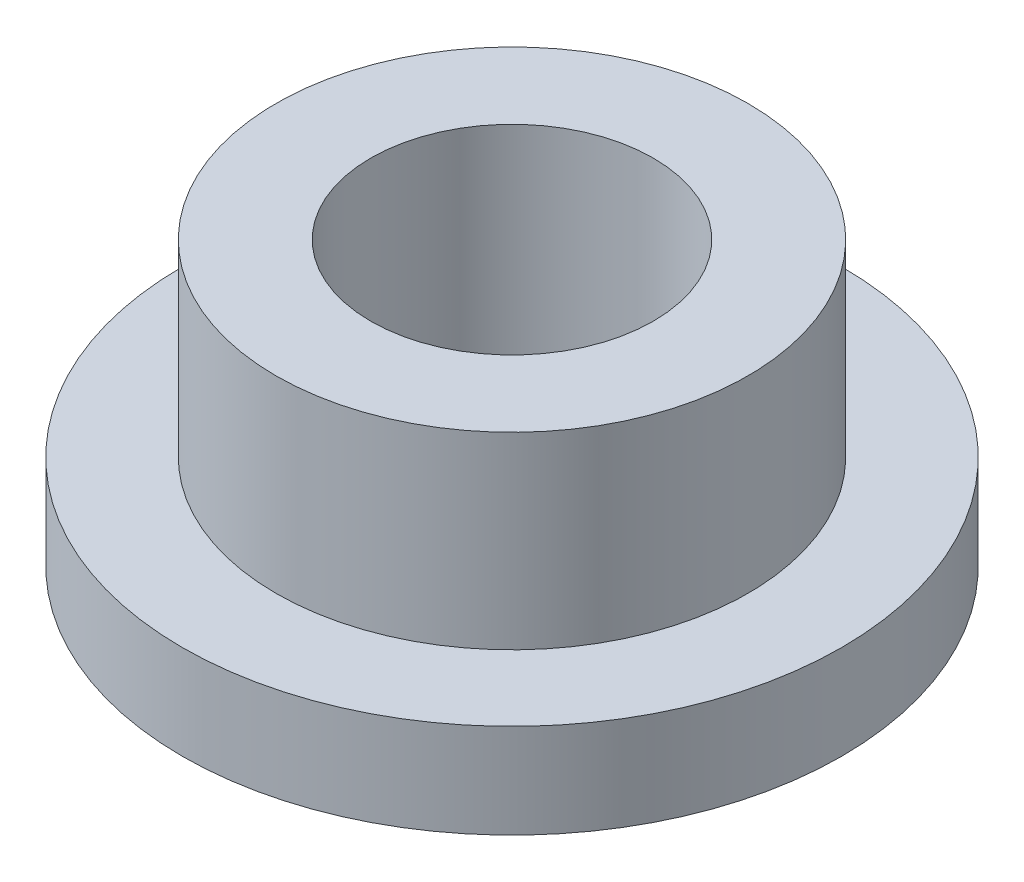
SolidWorks part; units mm, degrees
ref_plane "Front" through (0, 0, 0) normal (0, 0, 1) x (1, 0, 0)
ref_plane "Top" through (0, 0, 0) normal (0, 1, 0) x (1, 0, 0)
ref_plane "Right" through (0, 0, 0) normal (1, 0, 0) x (0, 0, -1)
sketch "Sketch1" plane through (0, 0, 0) normal (0, 1, 0) x (1, 0, 0)
  circle A0 centre (0, 0) radius 3
  circle A1 centre (0, 0) radius 5.01
  circle A2 centre (0, 0) radius 7
  dimension "ID" = 6
  dimension "OD" = 10.02
  dimension "FlangeOD" = 14
sketch "Sketch2" plane through (0, 0, 0) normal (0, 1, 0) x (1, 0, 0)
  circle A0 centre (0, 0) radius 3 construction
  circle A1 centre (0, 0) radius 5.01 construction
  circle A2 centre (0, 0) radius 3
  circle A3 centre (0, 0) radius 5.01
extrude "Boss-Extrude1" add sketch "Sketch2" along normal blind 6
sketch "Sketch3" plane through (0, 0, 0) normal (0, 1, 0) x (1, 0, 0)
  circle A0 centre (0, 0) radius 7 construction
  circle A1 centre (0, 0) radius 5.01 construction
  circle A2 centre (0, 0) radius 7
  circle A3 centre (0, 0) radius 5.01
extrude "Boss-Extrude2" add sketch "Sketch3" along normal blind 2
